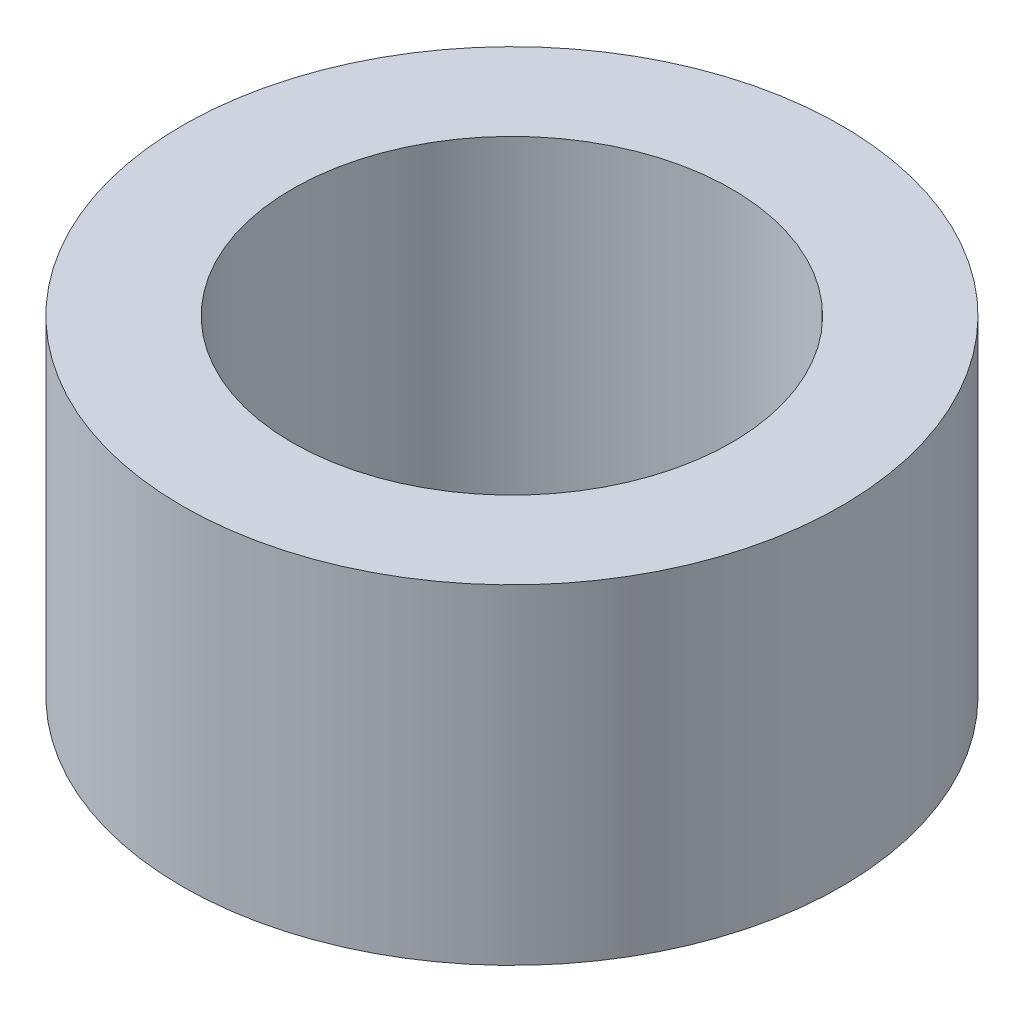
SolidWorks part; units mm, degrees
ref_plane "Front Plane" through (0, 0, 0) normal (0, 0, 1) x (1, 0, 0)
ref_plane "Top Plane" through (0, 0, 0) normal (0, 1, 0) x (1, 0, 0)
ref_plane "Right Plane" through (0, 0, 0) normal (1, 0, 0) x (0, 0, -1)
sketch "Sketch1" plane through (0, 0, 0) normal (0, 1, 0) x (1, 0, 0)
  circle A0 centre (0, 0) radius 3
  circle A1 centre (0, 0) radius 2
  dimension "D1" = 6
  dimension "D2" = 4
extrude "Boss-Extrude1" add sketch "Sketch1" along normal blind 3
